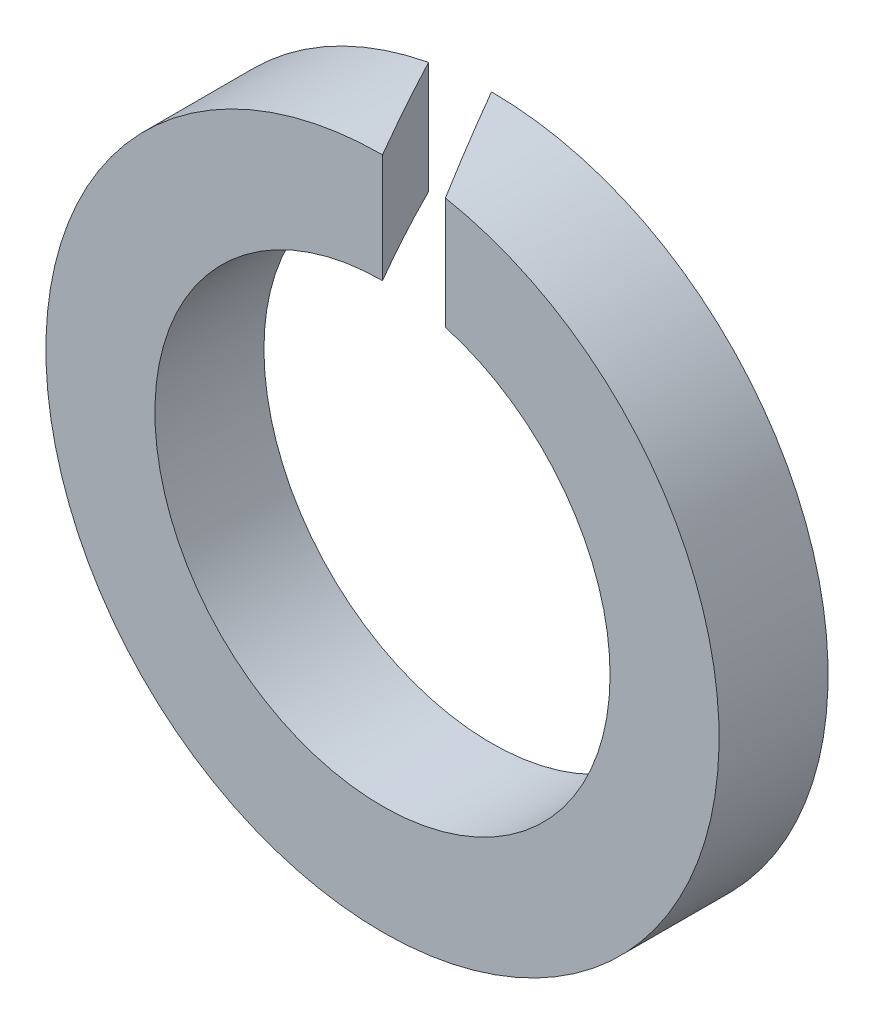
SolidWorks part; units mm, degrees
ref_plane "Front" through (0, 0, 0) normal (0, 0, 1) x (1, 0, 0)
ref_plane "Top" through (0, 0, 0) normal (0, 1, 0) x (1, 0, 0)
ref_plane "Right" through (0, 0, 0) normal (1, 0, 0) x (0, 0, -1)
sketch "Sketch1" plane through (0, 0, 0) normal (0, 0, 1) x (1, 0, 0)
  circle A0 centre (0, 0) radius 3.34
  circle A1 centre (0, 0) radius 4.94
  dimension "d" = 6.68
  dimension "b" = 1.6
extrude "Base-Extrude" add sketch "Sketch1" against normal blind 1.6
sketch "Sketch2" plane through (0, 0, 0) normal (0, 1, 0) x (1, 0, 0)
  line L0 (0, 1.6) -> (0.9238, 0)
  line L1 (0.9238, 0) -> (0, 0)
  line L3 (0, 0) -> (-0.9238, 1.6)
  line L5 (-0.9238, 1.6) -> (0, 1.6)
  line L7 (4.94, 1.6) -> (-4.94, 1.6) construction
  dimension "m" = 0.8
extrude "Cut-Extrude1" cut sketch "Sketch2" along normal through all
